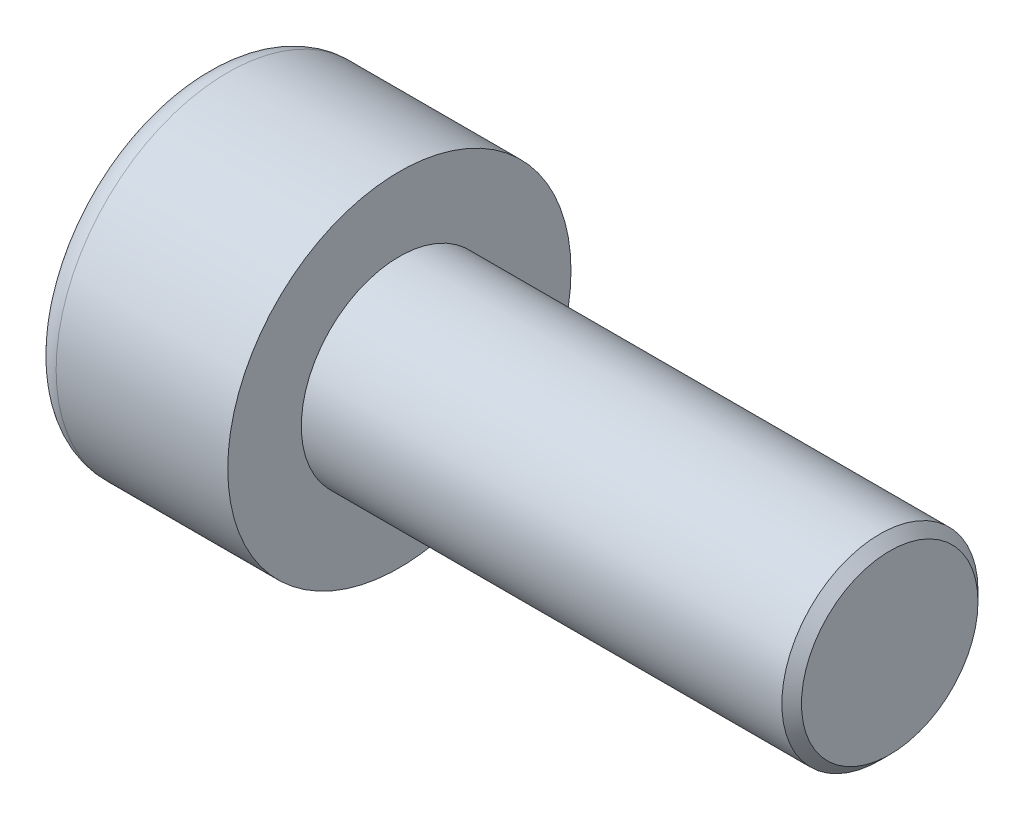
SolidWorks part; units mm, degrees
ref_plane "Front" through (0, 0, 0) normal (0, 0, 1) x (1, 0, 0)
ref_plane "Top" through (0, 0, 0) normal (0, 1, 0) x (1, 0, 0)
ref_plane "Right" through (0, 0, 0) normal (1, 0, 0) x (0, 0, -1)
sketch "Sketch1" plane through (0, 0, 0) normal (1, 0, 0) x (0, 0, -1)
  circle A0 centre (0, 0) radius 3.5
  dimension "dk" = 7
extrude "BaseHead" add sketch "Sketch1" along normal blind 4
sketch "Sketch2" plane through (4, 0, 0) normal (1, 0, 0) x (0, 0, -1)
  circle A0 centre (0, 0) radius 2
  dimension "d" = 4
extrude "BaseBody" add sketch "Sketch2" along normal blind 10
cosmetic thread "ThreadCosmetic1" parameters "b"=10, "D2"=3.242
sketch "Sketch3" plane through (0, 0, 0) normal (1, 0, 0) x (0, 0, -1)
  line L1 (1.7321, 0) -> (0.866, 1.5)
  line L2 (0.866, 1.5) -> (-0.866, 1.5)
  line L3 (-0.866, 1.5) -> (-1.7321, 0)
  line L4 (-1.7321, 0) -> (-0.866, -1.5)
  line L5 (-0.866, -1.5) -> (0.866, -1.5)
  line L6 (0.866, -1.5) -> (1.7321, 0)
  circle A0 centre (0, 0) radius 1.5 construction
  dimension "s" = 3
  dimension "e" = 3.4641
extrude "HexagonSocket" cut sketch "Sketch3" along normal blind 2
sketch "Sketch4" plane through (-4.1961, 0.75, 0) normal (0, 0, 1) x (-1, 0, 0)
  line L0 (-6.1961, 2.25) -> (-7.0622, 0.75)
  line L2 (-7.0622, 0.75) -> (-6.1961, 0.75)
  line L3 (-6.1961, 0.75) -> (-6.1961, 2.25)
  line L4 (-5.0351, 0.75) -> (0.839, 0.75) construction
  line L5 (-18.1961, 0.75) -> (-8.1961, 0.75) construction
  line L6 (-8.1961, 0.75) -> (-4.1961, 0.75) construction
  dimension "m" = 60
revolve "Cut-Revolve1" cut sketch "Sketch4" angle 360 about L4
fillet "HeadFillet" [suppressed] radius 0.2
fillet "TopFillet" radius 0.5 1 edges at (0, 0, -3.5)
chamfer "Chamfer1" distance 0.2 angle 45 1 edges at (14, 0, -2)
sketch "Sketch5" plane through (0, 0, 0) normal (0, 0, 1) x (1, 0, 0)
  line L0 (13.8, 1.6718) -> (13.9895, 2)
  line L1 (13.9895, 2) -> (13.9895, 2.379)
  line L2 (13.9895, 2.379) -> (13.6105, 2.379)
  line L3 (13.6105, 2.379) -> (13.6105, 2)
  line L4 (13.6105, 2) -> (13.8, 1.6718)
  line L5 (0, 0) -> (7.8886, 0) construction
  line L6 (13.8, -2) -> (13.8, 2) construction
  dimension "D1" = 4
  dimension "D2" = 0.379
revolve "Cut-Revolve10" [suppressed] cut sketch "Sketch5" angle 360 about L5
pattern_linear "LPattern10" [suppressed] count 22 spacing 0.4548 along (1, 0, 0)
equation "\"r1@TopFillet\" = \"d@Sketch2\" / 8"
equation "\"D1@Chamfer1\" = \"r@HeadFillet\""
equation "\"D1@Sketch5\" = \"d@Sketch2\""
equation "\"D2@Sketch5\" =  ( \"d@Sketch2\" - \"D2@ThreadCosmetic1\" )  / 2"
equation "\"D3@LPattern10\" = \"D2@Sketch5\" * 1.2"
equation "\"D1@LPattern10\" = \"b@ThreadCosmetic1\" / \"D3@LPattern10\""
